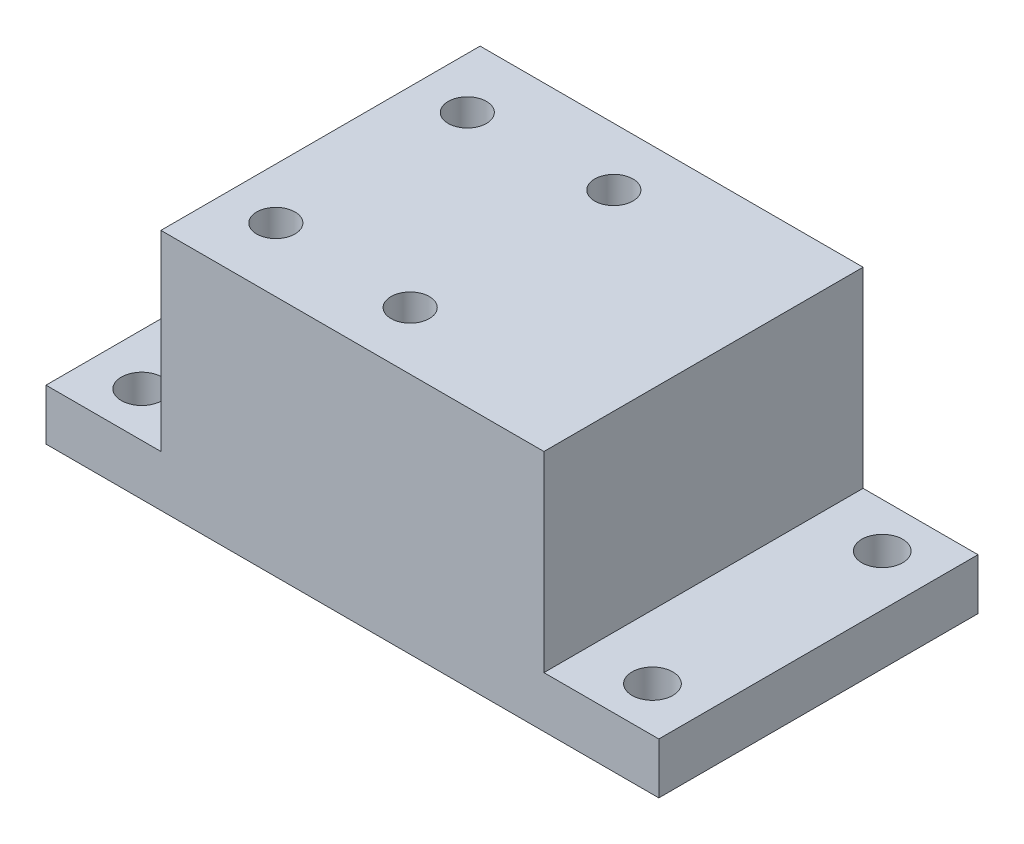
SolidWorks part; units mm, degrees
ref_plane "Спереди" through (0, 0, 0) normal (0, 0, 1) x (1, 0, 0)
ref_plane "Сверху" through (0, 0, 0) normal (0, 1, 0) x (1, 0, 0)
ref_plane "Справа" through (0, 0, 0) normal (1, 0, 0) x (0, 0, -1)
sketch "Sketch1" plane through (0, 0, 0) normal (0, 1, 0) x (1, 0, 0)
  line L1 (24, -12.5) -> (-24, -12.5)
  line L2 (24, -12.5) -> (24, 12.5)
  line L3 (24, 12.5) -> (-24, 12.5)
  line L4 (-24, -12.5) -> (-24, 12.5)
  line L5 (24, -12.5) -> (-24, 12.5) construction
  line L6 (24, 12.5) -> (-24, -12.5) construction
  point P0 (0, 0)
  dimension "D1" = 25
  dimension "D2" = 48
extrude "Boss-Extrude1" add sketch "Sketch1" along normal blind 4
sketch "Sketch2" plane through (0, 4, 0) normal (0, 1, 0) x (1, 0, 0)
  line L0 (24, 12.5) -> (-24, 12.5) construction
  line L1 (15, -12.5) -> (-15, -12.5)
  line L2 (15, -12.5) -> (15, 12.5)
  line L3 (15, 12.5) -> (-15, 12.5)
  line L4 (-15, -12.5) -> (-15, 12.5)
  line L5 (15, -12.5) -> (-15, 12.5) construction
  line L6 (15, 12.5) -> (-15, -12.5) construction
  point P0 (0, 0)
  dimension "D1" = 30
extrude "Boss-Extrude2" add sketch "Sketch2" along normal blind 15
sketch "Sketch3" plane through (0, 19, 0) normal (0, 1, 0) x (1, 0, 0)
  line L0 (0, 9.5) -> (0, 6.45) construction
  line L1 (0, -6.45) -> (0, -9.5) construction
  line L2 (0, 12.5) -> (0, -12.5) construction
  line L3 (15, 12.5) -> (-15, 12.5) construction
  line L4 (-15, -12.5) -> (15, -12.5) construction
  line L5 (15, 0) -> (-15, 0) construction
  line L6 (15, -12.5) -> (15, 12.5) construction
  line L7 (-15, 12.5) -> (-15, -12.5) construction
  line L8 (-11, 12.5) -> (-11, -12.5) construction
  circle A0 centre (0, 0) radius 9.5 construction
  circle A1 centre (0, 0) radius 6.45 construction
  circle A2 centre (0, 7.975) radius 1.5
  circle A3 centre (0, -7.975) radius 1.5
  circle A4 centre (-11, 7.5) radius 1.5
  circle A5 centre (-11, -7.5) radius 1.5
  dimension "D1" = 19
  dimension "D2" = 12.9
  dimension "D3" = 3
  dimension "D4" = 3
  dimension "D6" = 3
  dimension "D5" = 11
  dimension "D7" = 15
  dimension "D8" = 7.5
extrude "Cut-Extrude1" cut sketch "Sketch3" against normal through all
sketch "Sketch4" plane through (0, 0, 0) normal (0, -1, 0) x (1, 0, 0)
  line L1 (20, -9) -> (-20, -9) construction
  line L2 (20, -9) -> (20, 9) construction
  line L3 (20, 9) -> (-20, 9) construction
  line L4 (-20, -9) -> (-20, 9) construction
  line L5 (20, -9) -> (-20, 9) construction
  line L6 (20, 9) -> (-20, -9) construction
  circle A0 centre (-20, 9) radius 1.6
  circle A1 centre (20, 9) radius 1.6
  circle A2 centre (20, -9) radius 1.6
  circle A3 centre (-20, -9) radius 1.6
  point P0 (0, 0)
  dimension "D3" = 3.2
  dimension "D1" = 18
  dimension "D2" = 40
extrude "Cut-Extrude2" cut sketch "Sketch4" against normal through all
